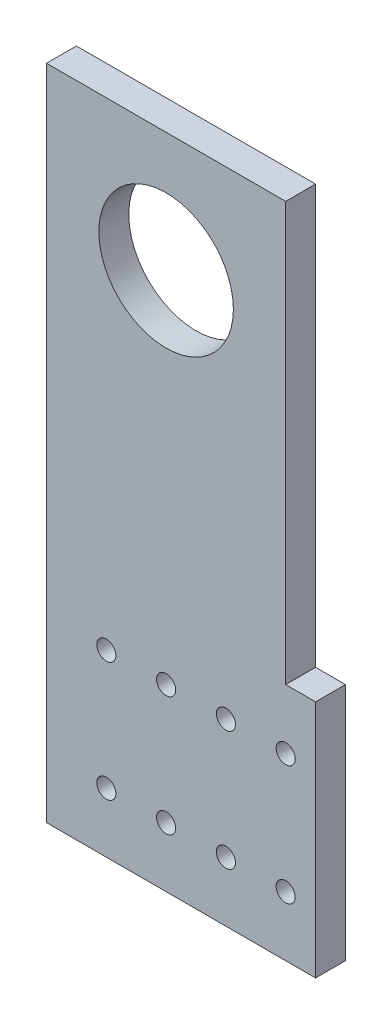
SolidWorks part; units mm, degrees
ref_plane "Front Plane" through (0, 0, 0) normal (0, 0, 1) x (1, 0, 0)
ref_plane "Top Plane" through (0, 0, 0) normal (0, 1, 0) x (1, 0, 0)
ref_plane "Right Plane" through (0, 0, 0) normal (1, 0, 0) x (0, 0, -1)
sketch "Sketch2" plane through (0, 0, 0) normal (0, 0, 1) x (1, 0, 0)
  line L0 (-125.792, -159.6416) -> (-74.992, -159.6416)
  line L11 (-74.992, -159.6416) -> (-68.642, -159.6416)
  line L12 (-68.642, -159.6416) -> (-68.642, -108.8416)
  line L13 (-68.642, -108.8416) -> (-74.992, -108.8416)
  line L14 (-74.992, -19.9416) -> (-74.992, -108.8416)
  line L15 (-125.792, -159.6416) -> (-125.792, -19.9416)
  line L16 (-125.792, -19.9416) -> (-74.992, -19.9416)
  dimension "D1" = 50.8
  dimension "D2" = 139.7
  dimension "D5" = 6.35
  dimension "D6" = 50.8
extrude "Boss-Extrude1" add sketch "Sketch2" along normal blind 6.35
sketch "Sketch3" plane through (0, 0, 6.35) normal (0, 0, 1) x (1, 0, 0)
  circle A0 centre (-100.392, -45.3516) radius 14.2875
  circle A2 centre (-87.692, -146.9416) radius 2.032
  circle A4 centre (-113.092, -146.9416) radius 2.032
  circle A5 centre (-100.392, -146.9416) radius 2.032
  circle A6 centre (-74.992, -146.9416) radius 2.032
  circle A7 centre (-113.092, -121.5416) radius 2.032
  circle A8 centre (-87.692, -121.5416) radius 2.032
  circle A9 centre (-74.992, -121.5416) radius 2.032
  circle A10 centre (-100.392, -121.5416) radius 2.032
  point P2 (-100.392, -45.3516)
  dimension "D1" = 28.575
  dimension "D5" = 4.064
  dimension "D8" = 4.064
  dimension "D9" = 4.064
  dimension "D10" = 4.064
  dimension "D3" = 4.064
  dimension "D7" = 4.064
  dimension "D6" = 4.064
  dimension "D11" = 4.064
  dimension "D2" = 12.7
extrude "Cut-Extrude1" cut sketch "Sketch3" against normal blind 6.35
sketch "Sketch4" plane through (0, 0, 6.35) normal (0, 0, 1) x (1, 0, 0)
  circle A0 centre (-113.092, -146.9416) radius 2.032
  circle A1 centre (-100.392, -146.9416) radius 2.032
  circle A2 centre (-87.692, -146.9416) radius 2.032
  circle A3 centre (-74.992, -146.9416) radius 2.032
